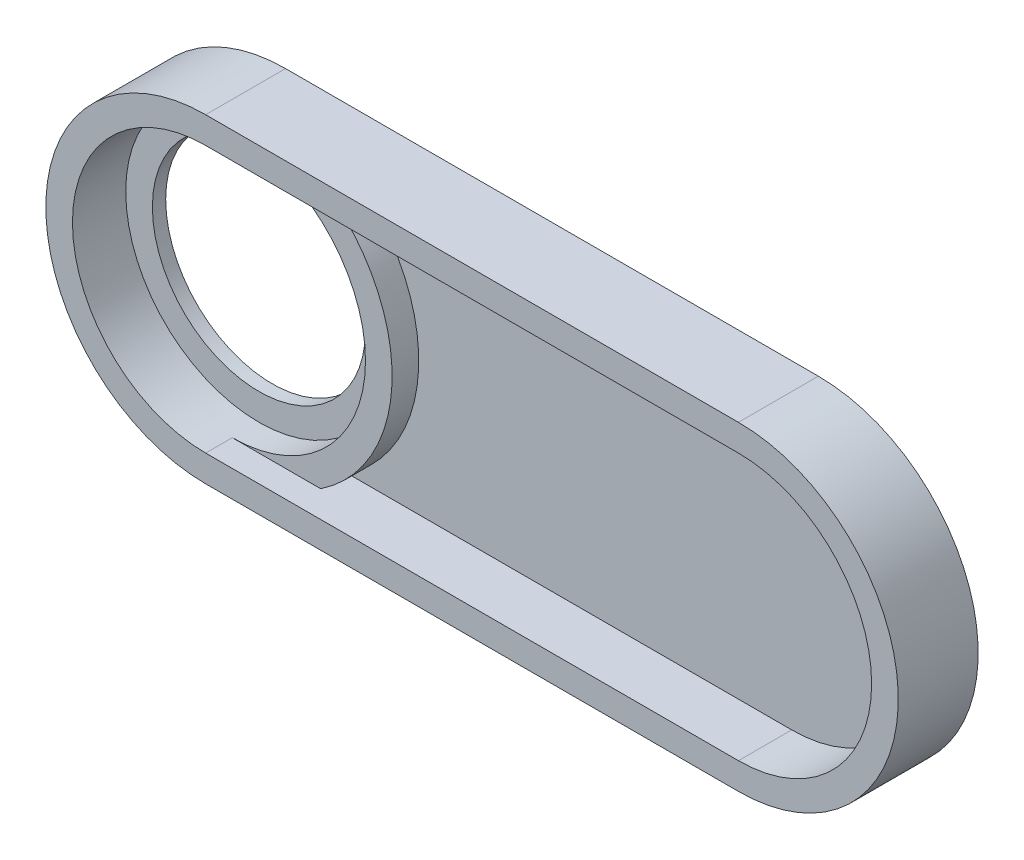
SolidWorks part; units mm, degrees
ref_plane "Front Plane" through (0, 0, 0) normal (0, 0, 1) x (1, 0, 0)
ref_plane "Top Plane" through (0, 0, 0) normal (0, 1, 0) x (1, 0, 0)
ref_plane "Right Plane" through (0, 0, 0) normal (1, 0, 0) x (0, 0, -1)
sketch "Sketch1" plane through (0, 0, 0) normal (0, 0, 1) x (1, 0, 0)
  line L0 (0, 0) -> (200, 0) construction
  line L1 (0, 60) -> (200, 60)
  line L2 (0, -60) -> (200, -60)
  arc A0 (0, 60) -> (0, -60) centre (0, 0) ccw
  arc A1 (200, -60) -> (200, 60) centre (200, 0) ccw
  circle A2 centre (0, 0) radius 40
  point P2 (100, 0)
  dimension "D3" = 80
  dimension "D1" = 60
  dimension "D2" = 200
extrude "Boss-Extrude1" add sketch "Sketch1" along normal blind 10
sketch "Sketch2" plane through (0, 0, 0) normal (0, 0, -1) x (-1, 0, 0)
  circle A0 centre (0, 0) radius 52.5
  dimension "D1" = 105
extrude "Cut-Extrude1" cut sketch "Sketch2" against normal blind 5
sketch "Sketch3" plane through (0, 0, 10) normal (0, 0, 1) x (1, 0, 0)
  circle A0 centre (0, 0) radius 40 construction
  circle A1 centre (0, 0) radius 40
  circle A2 centre (0, 0) radius 50
  circle A3 centre (0, 0) radius 60
  arc A4 (0, 60) -> (0, -60) centre (0, 0) ccw construction
  arc M1 (0, 60) -> (0, -60) centre (0, 0) ccw
  dimension "D1" = 100
extrude "Boss-Extrude2" add sketch "Sketch3" along normal blind 10 contours A3 A2 M1
sketch "Sketch4" plane through (0, 0, 10) normal (0, 0, 1) x (1, 0, 0)
  line L0 (0, -60) -> (200, -60) construction
  line L1 (200, 60) -> (0, 60) construction
  line L2 (0, -60) -> (200, -60)
  line L3 (200, 60) -> (0, 60)
  line L4 (200, 50) -> (0, 50)
  line L5 (0, -50) -> (200, -50)
  circle A0 centre (0, 0) radius 60 construction
  arc A1 (200, -60) -> (200, 60) centre (200, 0) ccw construction
  arc A2 (0, 60) -> (0, -60) centre (0, 0) ccw
  arc A3 (200, -60) -> (200, 60) centre (200, 0) ccw
  arc A4 (0, 50) -> (0, -50) centre (0, 0) ccw
  arc A5 (200, -50) -> (200, 50) centre (200, 0) ccw
  dimension "D1" = 10
extrude "Boss-Extrude3" add sketch "Sketch4" along normal blind 20
